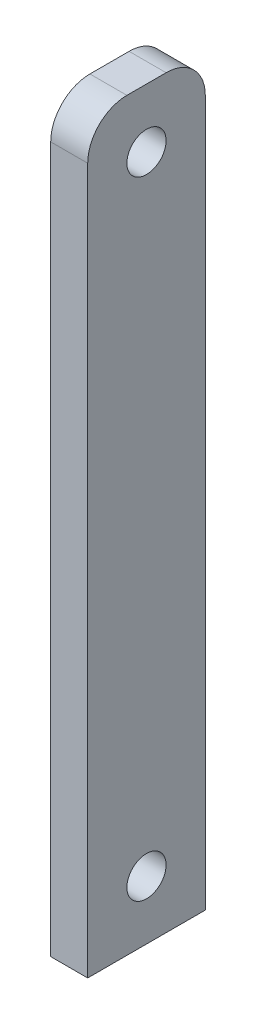
SolidWorks part; units mm, degrees
ref_plane "Front Plane" through (0, 0, 0) normal (0, 0, 1) x (1, 0, 0)
ref_plane "Top Plane" through (0, 0, 0) normal (0, 1, 0) x (1, 0, 0)
ref_plane "Right Plane" through (0, 0, 0) normal (1, 0, 0) x (0, 0, -1)
sketch "Sketch1" plane through (0, 0, 0) normal (1, 0, 0) x (0, 0, -1)
  line L0 (0, 0) -> (0, 50.8) construction
  line L2 (-4.7625, -4.7625) -> (4.7625, -4.7625)
  line L3 (-4.7625, -4.7625) -> (-4.7625, 55.5625)
  line L4 (-4.7625, 55.5625) -> (4.7625, 55.5625)
  line L5 (4.7625, -4.7625) -> (4.7625, 55.5625)
  line L6 (-4.7625, -4.7625) -> (4.7625, 55.5625) construction
  line L7 (-4.7625, 55.5625) -> (4.7625, -4.7625) construction
  circle A0 centre (0, 0) radius 1.5875
  circle A1 centre (0, 50.8) radius 1.5875
  point P5 (0, 25.4)
  dimension "D1" = 3.175
  dimension "D2" = 50.8
  dimension "D3" = 4.7625
  dimension "D4" = 9.525
extrude "Extrude1" add sketch "Sketch1" along normal mid plane 2.9972
fillet "Fillet1" radius 3.175 2 edges at (0, 55.5625, -4.7625) (0, 55.5625, 4.7625)
